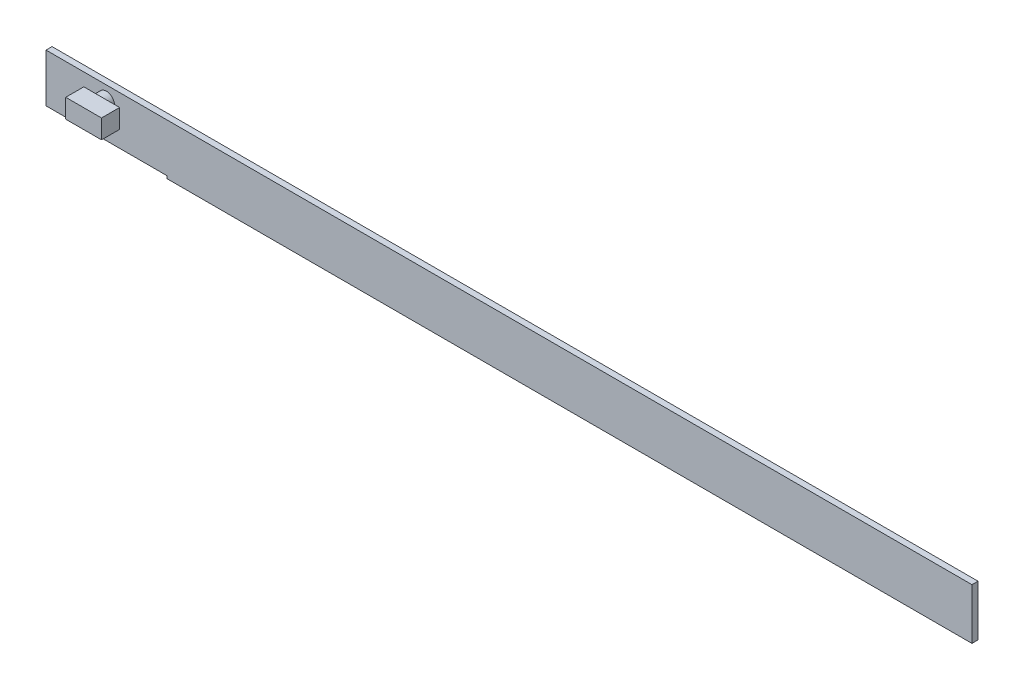
SolidWorks part; units mm, degrees
ref_plane "Front Plane" through (0, 0, 0) normal (0, 0, 1) x (1, 0, 0)
ref_plane "Top Plane" through (0, 0, 0) normal (0, 1, 0) x (1, 0, 0)
ref_plane "Right Plane" through (0, 0, 0) normal (1, 0, 0) x (0, 0, -1)
sketch "Sketch2" plane through (0, 0, 0) normal (0, 0, 1) x (1, 0, 0)
  line L1 (-47.8692, 21.2481) -> (206.1308, 21.2481)
  line L2 (-47.8692, 21.2481) -> (-47.8692, 8.5481)
  line L3 (-47.8692, 8.5481) -> (206.1308, 8.5481)
  line L4 (206.1308, 21.2481) -> (206.1308, 8.5481)
  dimension "D1" = 12.7
  dimension "D2" = 254
extrude "Boss-Extrude1" add sketch "Sketch2" along normal blind 101.6
sketch "Sketch3" plane through (0, 21.2481, 0) normal (0, 1, 0) x (1, 0, 0)
  circle A0 centre (79.1308, -28.4831) radius 17.1408
extrude "Boss-Extrude2" add sketch "Sketch3" along normal blind 19.05
sketch "Sketch4" plane through (0, 40.2981, 0) normal (0, 1, 0) x (1, 0, 0)
  line L1 (50.7675, -8.111) -> (126.0034, -8.111)
  line L2 (50.7675, -8.111) -> (50.7675, -48.0661)
  line L3 (50.7675, -48.0661) -> (126.0034, -48.0661)
  line L4 (126.0034, -8.111) -> (126.0034, -48.0661)
extrude "Boss-Extrude3" add sketch "Sketch4" along normal blind 38.1
scale "Scale2" scale about centroid uniform scaling yes scale factor 0.00375
move or copy body "rotate" bodies to move or copy 105 copy no rotation origin (0, 33.6669, 26.5501) rotation axis (1, 0, 0) rotation angle 90
move or copy body "-4 x" bodies to move or copy 106 copy no translate (-101.6, 0, 0)
move or copy body "-2 y" bodies to move or copy 117 copy no translate (0, -55.88, 0)
move or copy body "-2.1z" bodies to move or copy 121 copy no translate (0, 0, -30.48)
sketch "Sketch6" plane through (0, -39.7871, 0) normal (0, 1, 0) x (1, 0, 0)
  line L1 (-19.6967, 11.0887) -> (-13.3467, 11.0887)
  line L2 (-19.6967, 11.0887) -> (-19.6967, 11.0411)
  line L3 (-19.6967, 11.0411) -> (-13.3467, 11.0411)
  line L4 (-13.3467, 11.0887) -> (-13.3467, 11.0411)
  dimension "D1" = 6.35
extrude "Boss-Extrude6" add sketch "Sketch6" against normal blind 0.4013
